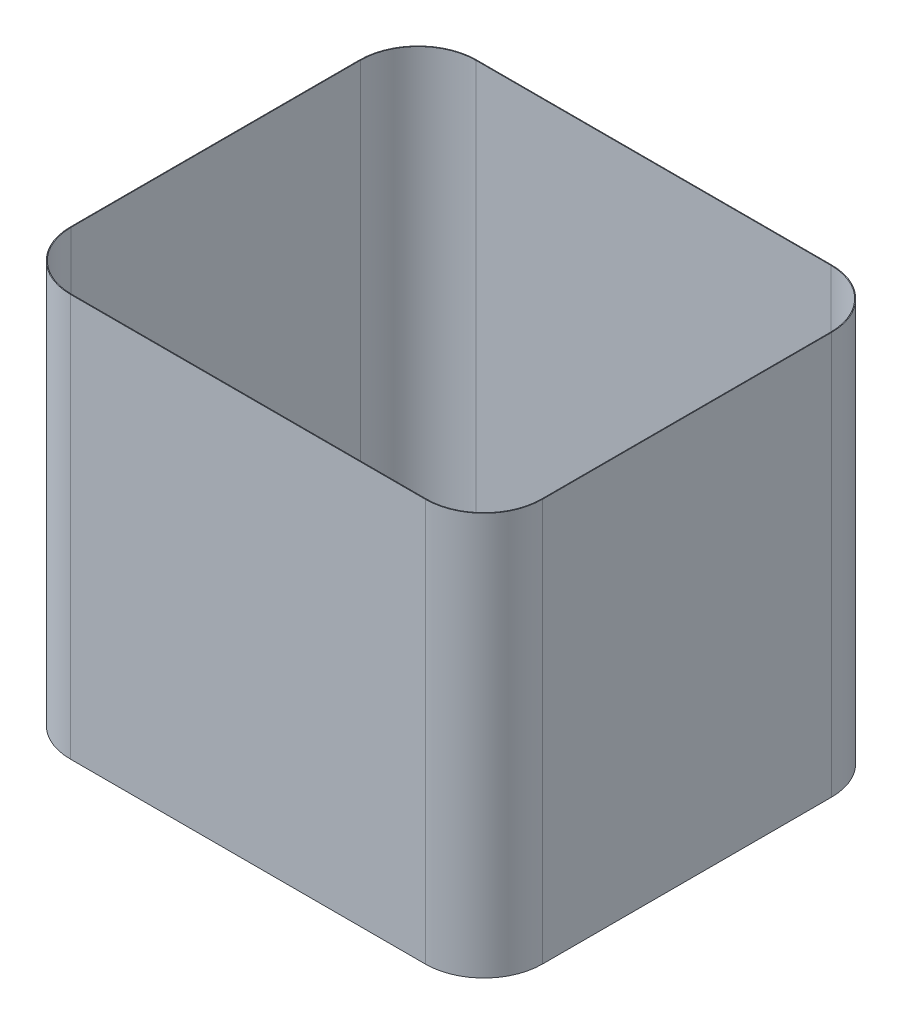
SolidWorks part; units mm, degrees
ref_plane "Front" through (0, 0, 0) normal (0, 0, 1) x (1, 0, 0)
ref_plane "Top" through (0, 0, 0) normal (0, 1, 0) x (1, 0, 0)
ref_plane "Right" through (0, 0, 0) normal (1, 0, 0) x (0, 0, -1)
sketch "Sketch1" plane through (0, 0, 0) normal (0, 1, 0) x (1, 0, 0)
  line L0 (-203.2, -406.4) -> (1028.7, -406.4)
  line L1 (0, 0) -> (825.5, 0) construction
  line L2 (0, 0) -> (0, 596.9) construction
  line L3 (0, 596.9) -> (825.5, 596.9) construction
  line L4 (825.5, 0) -> (825.5, 596.9) construction
  line L5 (0, 0) -> (825.5, 596.9) construction
  line L6 (0, 596.9) -> (825.5, 0) construction
  line L7 (1231.9, -203.2) -> (1231.9, 800.1)
  line L8 (-203.2, 1003.3) -> (1028.7, 1003.3)
  line L9 (-406.4, -203.2) -> (-406.4, 800.1)
  line L10 (-406.4, -406.4) -> (1231.9, -406.4) construction
  line L11 (-406.4, -406.4) -> (-406.4, 1003.3) construction
  line L12 (1231.9, -406.4) -> (1231.9, 1003.3) construction
  line L13 (-406.4, 1003.3) -> (1231.9, 1003.3) construction
  arc A0 (-203.2, -406.4) -> (-406.4, -203.2) centre (-203.2, -203.2) cw
  arc A1 (1028.7, -406.4) -> (1231.9, -203.2) centre (1028.7, -203.2) ccw
  arc A2 (1231.9, 800.1) -> (1028.7, 1003.3) centre (1028.7, 800.1) ccw
  arc A3 (-203.2, 1003.3) -> (-406.4, 800.1) centre (-203.2, 800.1) ccw
  point P4 (412.75, 298.45)
  dimension "D4" = 203.2
  dimension "D1" = 596.9
  dimension "D2" = 825.5
  dimension "D3" = 406.4
extrude "Boss-Extrude1" add sketch "Sketch1" along normal blind 1397
shell "Shell1" thickness 2.54
sketch "Sketch3" plane through (0, 1394.46, 0) normal (0, -1, 0) x (1, 0, 0)
  line L4 (-403.86, 203.2) -> (-403.86, -800.1)
  line L5 (-203.2, -1000.76) -> (1028.7, -1000.76)
  line L6 (1229.36, -800.1) -> (1229.36, 203.2)
  line L7 (1028.7, 403.86) -> (-203.2, 403.86)
  line L8 (-403.86, 203.2) -> (-403.86, -800.1)
  line L9 (-203.2, -1000.76) -> (1028.7, -1000.76)
  line L10 (1229.36, -800.1) -> (1229.36, 203.2)
  line L11 (1028.7, 403.86) -> (-203.2, 403.86)
  arc A4 (-203.2, 403.86) -> (-403.86, 203.2) centre (-203.2, 203.2) ccw
  arc A5 (-403.86, -800.1) -> (-203.2, -1000.76) centre (-203.2, -800.1) ccw
  arc A6 (1028.7, -1000.76) -> (1229.36, -800.1) centre (1028.7, -800.1) ccw
  arc A7 (1229.36, 203.2) -> (1028.7, 403.86) centre (1028.7, 203.2) ccw
  arc A8 (-203.2, 403.86) -> (-403.86, 203.2) centre (-203.2, 203.2) ccw
  arc A9 (-403.86, -800.1) -> (-203.2, -1000.76) centre (-203.2, -800.1) ccw
  arc A10 (1028.7, -1000.76) -> (1229.36, -800.1) centre (1028.7, -800.1) ccw
  arc A11 (1229.36, 203.2) -> (1028.7, 403.86) centre (1028.7, 203.2) ccw
  dimension "D1" = 0
extrude "Cut-Extrude3" cut sketch "Sketch3" against normal up to next
